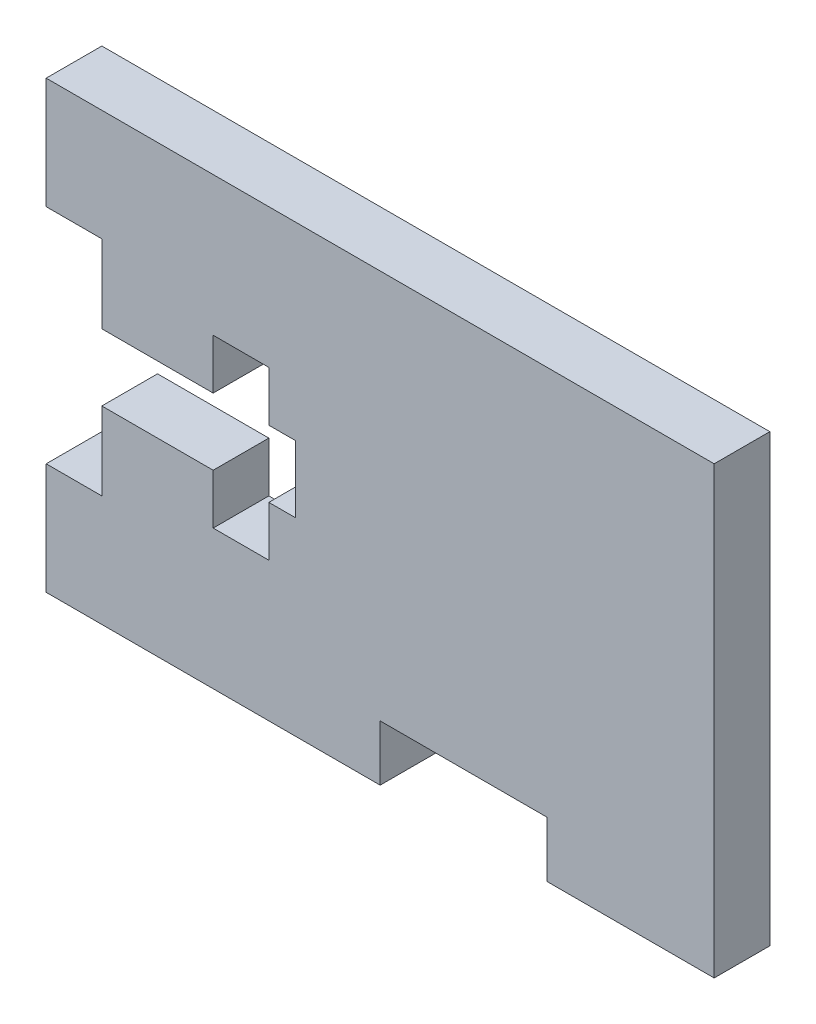
SolidWorks part; units mm, degrees
ref_plane "Front Plane" through (0, 0, 0) normal (0, 0, 1) x (1, 0, 0)
ref_plane "Top Plane" through (0, 0, 0) normal (0, 1, 0) x (1, 0, 0)
ref_plane "Right Plane" through (0, 0, 0) normal (1, 0, 0) x (0, 0, -1)
sketch "Sketch1" plane through (0, 0, 0) normal (0, 0, 1) x (1, 0, 0)
  line L0 (-4.826, 0) -> (19.05, 0) construction
  line L1 (-19.05, 12.7) -> (19.05, 12.7)
  line L2 (-19.05, 12.7) -> (-19.05, 6.35)
  line L3 (-19.05, -12.7) -> (0, -12.7)
  line L4 (19.05, 12.7) -> (19.05, -12.7)
  line L5 (0, 12.7) -> (0, -12.7) construction
  line L6 (-19.05, 6.35) -> (-15.875, 6.35)
  line L7 (-15.875, 6.35) -> (-15.875, 1.905)
  line L8 (-15.875, 1.905) -> (-9.525, 1.905)
  line L9 (-9.525, 1.905) -> (-9.525, 4.7625)
  line L10 (-9.525, 4.7625) -> (-6.35, 4.7625)
  line L11 (-6.35, 4.7625) -> (-6.35, 1.905)
  line L12 (-6.35, 1.905) -> (-4.826, 1.905)
  line L13 (-4.826, 1.905) -> (-4.826, -1.905)
  line L14 (-6.35, -1.905) -> (-4.826, -1.905)
  line L15 (-6.35, -4.7625) -> (-6.35, -1.905)
  line L16 (-9.525, -4.7625) -> (-6.35, -4.7625)
  line L17 (-9.525, -1.905) -> (-9.525, -4.7625)
  line L18 (-15.875, -1.905) -> (-9.525, -1.905)
  line L19 (-15.875, -6.35) -> (-15.875, -1.905)
  line L20 (-19.05, -6.35) -> (-15.875, -6.35)
  line L21 (0, -12.7) -> (0, -9.525)
  line L22 (0, -9.525) -> (9.525, -9.525)
  line L23 (9.525, -9.525) -> (9.525, -12.7)
  line L24 (-19.05, -6.35) -> (-19.05, -12.7)
  line L25 (9.525, -12.7) -> (19.05, -12.7)
  point P19 (-4.826, 0)
  dimension "D1" = 25.4
  dimension "D2" = 12.7
  dimension "D3" = 38.1
  dimension "D4" = 19.05
  dimension "D5" = 3.175
  dimension "D6" = 3.175
  dimension "D7" = 14.224
  dimension "D8" = 12.7
  dimension "D9" = 1.905
  dimension "D10" = 4.7625
  dimension "D11" = 6.35
  dimension "D12" = 3.175
  dimension "D13" = 9.525
extrude "Boss-Extrude1" add sketch "Sketch1" along normal blind 3.175
equation "\"THICK\"= 1 / 8in"
